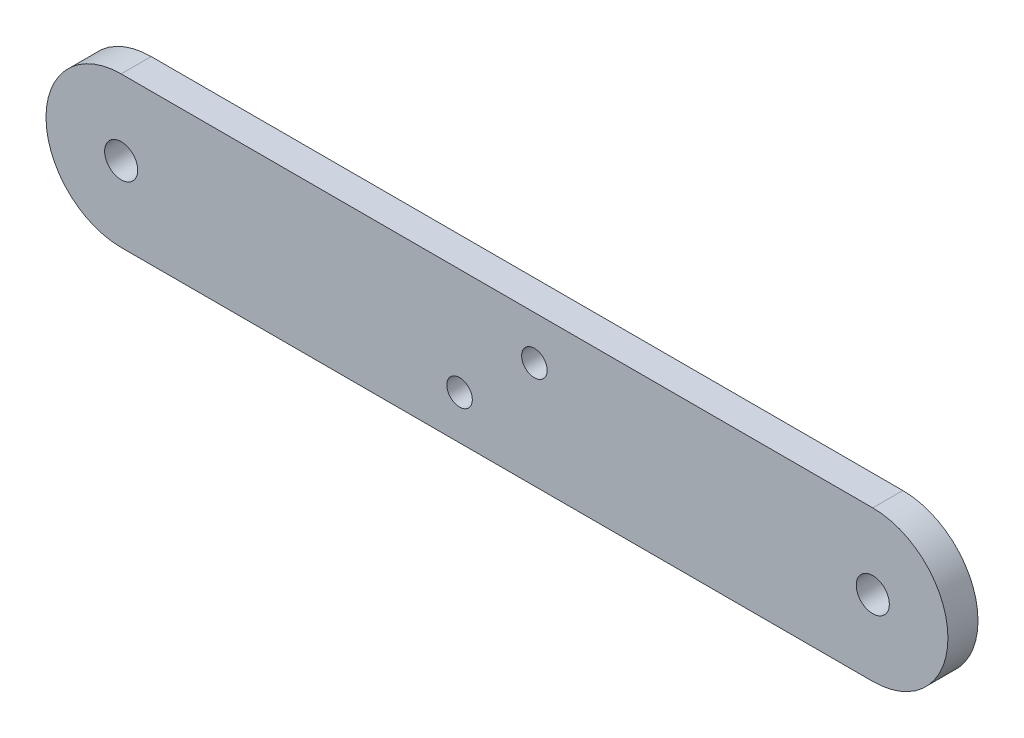
SolidWorks part; units mm, degrees
ref_plane "Plan de face" through (0, 0, 0) normal (0, 0, 1) x (1, 0, 0)
ref_plane "Plan de dessus" through (0, 0, 0) normal (0, 1, 0) x (1, 0, 0)
ref_plane "Plan de droite" through (0, 0, 0) normal (1, 0, 0) x (0, 0, -1)
sketch "Esquisse1" plane through (0, 0, 0) normal (0, 0, 1) x (1, 0, 0)
  line L0 (0, 0) -> (100, 0) construction
  line L1 (0, 0) -> (100, 0) construction
  line L2 (0, 10) -> (100, 10)
  line L3 (0, -10) -> (100, -10)
  line L4 (50, 0) -> (61.9175, 10) construction
  line L5 (50, 0) -> (38.0825, -10) construction
  line L6 (50, 0) -> (41.609, 10) construction
  circle A0 centre (0, 0) radius 2.2
  circle A1 centre (100, 0) radius 2.2
  arc A2 (0, 10) -> (0, -10) centre (0, 0) ccw
  arc A3 (100, -10) -> (100, 10) centre (100, 0) ccw
  circle A4 centre (54.9793, 4.1781) radius 1.7
  circle A5 centre (45.0207, -4.1781) radius 1.7
  point P6 (50, 0)
  point P18 (0, 0)
  dimension "D1" = 4.4
  dimension "D5" = 3.4
  dimension "D2" = 100
  dimension "D3" = 20
  dimension "D4" = 40
  dimension "D6" = 13
extrude "Boss.-Extru.1" add sketch "Esquisse1" along normal blind 4
